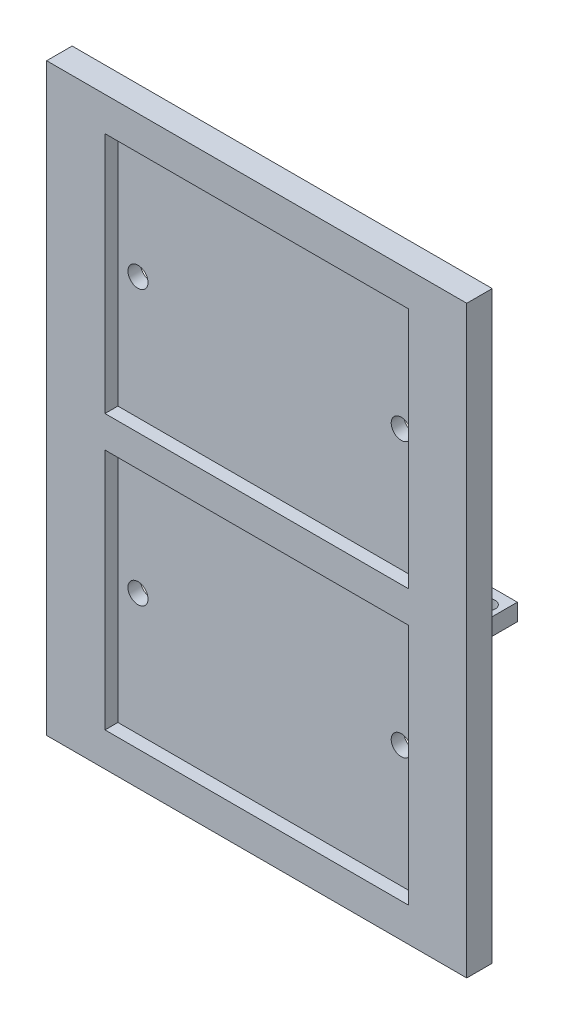
SolidWorks part; units mm, degrees
ref_plane "Front Plane" through (0, 0, 0) normal (0, 0, 1) x (1, 0, 0)
ref_plane "Top Plane" through (0, 0, 0) normal (0, 1, 0) x (1, 0, 0)
ref_plane "Right Plane" through (0, 0, 0) normal (1, 0, 0) x (0, 0, -1)
sketch "Sketch4" plane through (0, 0, 0) normal (0, 0, 1) x (1, 0, 0)
  line L8 (-22.7709, 76.1547) -> (22.7709, 76.1547)
  line L9 (25.3094, 73.5272) -> (22.8585, 2.4525)
  line L10 (20.32, 0) -> (-20.32, 0)
  line L11 (0, 76.1547) -> (0, 0) construction
  line L12 (-25.3094, 73.5272) -> (-22.8585, 2.4525)
  arc A0 (22.8585, 2.4525) -> (20.32, 0) centre (20.32, 2.54) cw
  arc A1 (22.7709, 76.1547) -> (25.3094, 73.5272) centre (22.7709, 73.6147) cw
  arc A2 (-22.8585, 2.4525) -> (-20.32, 0) centre (-20.32, 2.54) ccw
  arc A3 (-22.7709, 76.1547) -> (-25.3094, 73.5272) centre (-22.7709, 73.6147) ccw
  circle A4 centre (0, 58.5396) radius 3.75
  circle A5 centre (0, 21.6223) radius 12.75
  point P6 (22.7739, 0)
  point P9 (25.4, 76.1547)
  dimension "D2" = 76.2
  dimension "D3" = 2.54
  dimension "D5" = 7.5
  dimension "D6" = 24.7778
  dimension "D7" = 25.5
  dimension "D8" = 23.5056
  dimension "D1" = 25.4
  dimension "D4" = 40.64
sketch "Sketch5" plane through (0, 0, 0) normal (0, 0, 1) x (1, 0, 0)
  line L0 (-25.4, 0) -> (25.4, 0)
  line L2 (25.4, 76.2) -> (-25.4, 76.2)
  line L3 (0, 76.2) -> (0, 0) construction
  line L4 (-25.4, 0) -> (-25.4, 76.2)
  line L5 (-25.4, 62.3349) -> (-29.4, 62.3349)
  line L6 (-29.4, 62.3349) -> (-29.4, 55.9793)
  line L7 (-29.4, 55.9793) -> (-25.4, 55.9793)
  line L8 (25.4, 76.2) -> (25.4, 62.3084)
  line L9 (25.4, 0) -> (25.4, 42.703)
  line L10 (25.4, 62.3084) -> (47.1877, 62.3084)
  line L11 (25.4, 42.703) -> (47.1877, 42.703)
  line L12 (47.1877, 62.3084) -> (89.4265, 20.0696)
  line L13 (47.1877, 62.3084) -> (47.1877, 42.703) construction
  line L14 (47.1877, 42.703) -> (79.6238, 10.2669)
  line L15 (89.4265, 20.0696) -> (79.6238, 10.2669) construction
  line L16 (79.6238, 10.2669) -> (72.5193, 3.1623)
  line L18 (47.1877, 52.5057) -> (89.4265, 10.2669) construction
  line L19 (72.5193, 3.1623) -> (77.4206, -1.7391)
  line L20 (77.4206, -1.7391) -> (89.4265, 10.2669)
  line L21 (89.4265, 20.0696) -> (96.5311, 27.1741)
  line L22 (96.5311, 27.1741) -> (101.4325, 22.2728)
  line L23 (101.4325, 22.2728) -> (89.4265, 10.2669)
  arc A0 (-25.4, 34.3485) -> (-25.4, 8.8723) centre (-25.4, 21.6104) ccw
  point P12 (-27.4, 55.9793)
  dimension "D3" = 12.7381
  dimension "D4" = 8.8723
  dimension "D8" = 21.6308
  dimension "D1" = 50.8
  dimension "D2" = 76.2
  dimension "D5" = 4
  dimension "D6" = 6.3556
  dimension "D7" = 13.8651
  dimension "D9" = 45
  dimension "D10" = 59.7348
  dimension "D11" = 21.7877
  dimension "D12" = 19.6054
  dimension "D13" = 45.8717
  dimension "D14" = 45
  dimension "D15" = 10.0474
  dimension "D16" = 6.9316
  dimension "D17" = 16.9789
  dimension "D18" = 13.8916
  dimension "D19" = 6.9316
  dimension "D20" = 10.0474
  dimension "D21" = 16.9789
sketch "Sketch12" plane through (0, 0, 0) normal (0, 0, 1) x (1, 0, 0)
  line L0 (-31.4071, 43.688) -> (31.4071, 43.688)
  line L1 (-31.4071, 43.688) -> (-31.4071, -43.688)
  line L2 (31.4071, 43.688) -> (31.4071, -43.688)
  line L3 (-31.4071, -43.688) -> (31.4071, -43.688)
  dimension "D1" = 62.8142
  dimension "D2" = 87.376
  dimension "D3" = 43.688
  dimension "D4" = 31.4071
extrude "Boss-Extrude5" add sketch "Sketch12" against normal blind 3.81
ref_plane "Plane2" through (0, 0, 0) normal (0, 0, 1) x (1, 0, 0)
sketch "Sketch22" plane through (0, 0, -3.81) normal (0, 0, -1) x (-1, 0, 0)
  line L0 (-30.0854, -0.127) -> (-26.2754, -0.127)
  line L1 (-30.0854, -0.127) -> (-30.0854, -2.667)
  line L2 (-26.2754, -0.127) -> (-26.2754, -2.667)
  line L3 (-30.0854, -2.667) -> (-26.2754, -2.667)
  line L4 (0, 43.688) -> (0, -43.688) construction
  line L5 (-31.4071, 43.688) -> (31.4071, 43.688) construction
  line L6 (31.4071, -43.688) -> (-31.4071, -43.688) construction
  line L7 (30.0854, -2.667) -> (26.2754, -2.667)
  line L8 (30.0854, -0.127) -> (30.0854, -2.667)
  line L9 (30.0854, -0.127) -> (26.2754, -0.127)
  line L10 (26.2754, -0.127) -> (26.2754, -2.667)
  line L11 (-31.4071, -43.688) -> (-31.4071, 43.688) construction
  dimension "D1" = 3.81
  dimension "D2" = 2.54
  dimension "D3" = 1.3217
  dimension "D4" = 43.815
extrude "Boss-Extrude6" add sketch "Sketch22" along normal blind 5.08
sketch "Sketch23" plane through (0, -0.127, 0) normal (0, 1, 0) x (1, 0, 0)
  line L0 (26.2754, 6.35) -> (30.0854, 6.35) construction
  line L1 (26.2754, 8.89) -> (26.2754, 3.81) construction
  line L2 (30.0854, 8.89) -> (30.0854, 3.81) construction
  line L3 (-30.0854, 6.35) -> (-26.2754, 6.35) construction
  line L4 (-30.0854, 8.89) -> (-30.0854, 3.81) construction
  line L5 (-26.2754, 8.89) -> (-26.2754, 3.81) construction
  circle A0 centre (28.1804, 6.35) radius 1.1303
  circle A1 centre (-28.3626, 6.35) radius 1.1303
  dimension "D1" = 2.2606
  dimension "D2" = 2.2606
  dimension "D3" = 1.7228
extrude "Cut-Extrude5" cut sketch "Sketch23" against normal blind 5.08
sketch "Sketch25" plane through (0, 0, 0) normal (0, 0, 1) x (1, 0, 0)
  line L0 (22.6822, 38.608) -> (22.6822, 2.3622)
  line L1 (22.6822, 38.608) -> (-22.6822, 38.608)
  line L2 (22.6822, 2.3622) -> (-22.6822, 2.3622)
  line L3 (-22.6822, 38.608) -> (-22.6822, 2.3622)
  line L4 (31.4071, -43.688) -> (31.4071, 43.688) construction
  line L5 (-31.4071, 43.688) -> (-31.4071, -43.688) construction
  line L6 (31.4071, 43.688) -> (-31.4071, 43.688) construction
  line L7 (31.4071, 0) -> (-31.4071, 0) construction
  line L8 (-22.6822, -38.608) -> (-22.6822, -2.3622)
  line L9 (22.6822, -38.608) -> (-22.6822, -38.608)
  line L10 (22.6822, -38.608) -> (22.6822, -2.3622)
  line L11 (22.6822, -2.3622) -> (-22.6822, -2.3622)
  dimension "D1" = 8.7249
  dimension "D2" = 8.7249
  dimension "D3" = 5.08
  dimension "D4" = 36.2458
extrude "Cut-Extrude6" cut sketch "Sketch25" against normal blind 1.9304
sketch "Sketch26" plane through (0, 0, -1.9304) normal (0, 0, 1) x (1, 0, 0)
  line L0 (0, 38.608) -> (0, 2.3622) construction
  line L1 (22.6822, 38.608) -> (-22.6822, 38.608) construction
  line L2 (-22.6822, 2.3622) -> (22.6822, 2.3622) construction
  line L3 (0, 2.3622) -> (0, -38.608) construction
  line L4 (-22.6822, -38.608) -> (22.6822, -38.608) construction
  line L5 (22.6822, -2.3622) -> (-22.6822, -2.3622) construction
  line L6 (22.6822, 2.3622) -> (22.6822, 38.608) construction
  line L8 (-31.4071, 0) -> (31.4071, 0) construction
  line L9 (-31.4071, 43.688) -> (-31.4071, -43.688) construction
  line L10 (31.4071, -43.688) -> (31.4071, 43.688) construction
  line L12 (22.6822, -38.608) -> (22.6822, -2.3622) construction
  circle A0 centre (19.6822, 20.608) radius 1.5
  circle A1 centre (19.6822, -20.3622) radius 1.5
  circle A2 centre (-19.6822, -20.3622) radius 1.5
  circle A3 centre (-19.6822, 20.608) radius 1.5
  dimension "D1" = 3
  dimension "D2" = 3
  dimension "D3" = 18
  dimension "D4" = 18
  dimension "D5" = 3
  dimension "D6" = 3
extrude "Cut-Extrude7" cut sketch "Sketch26" against normal blind 1.9304
